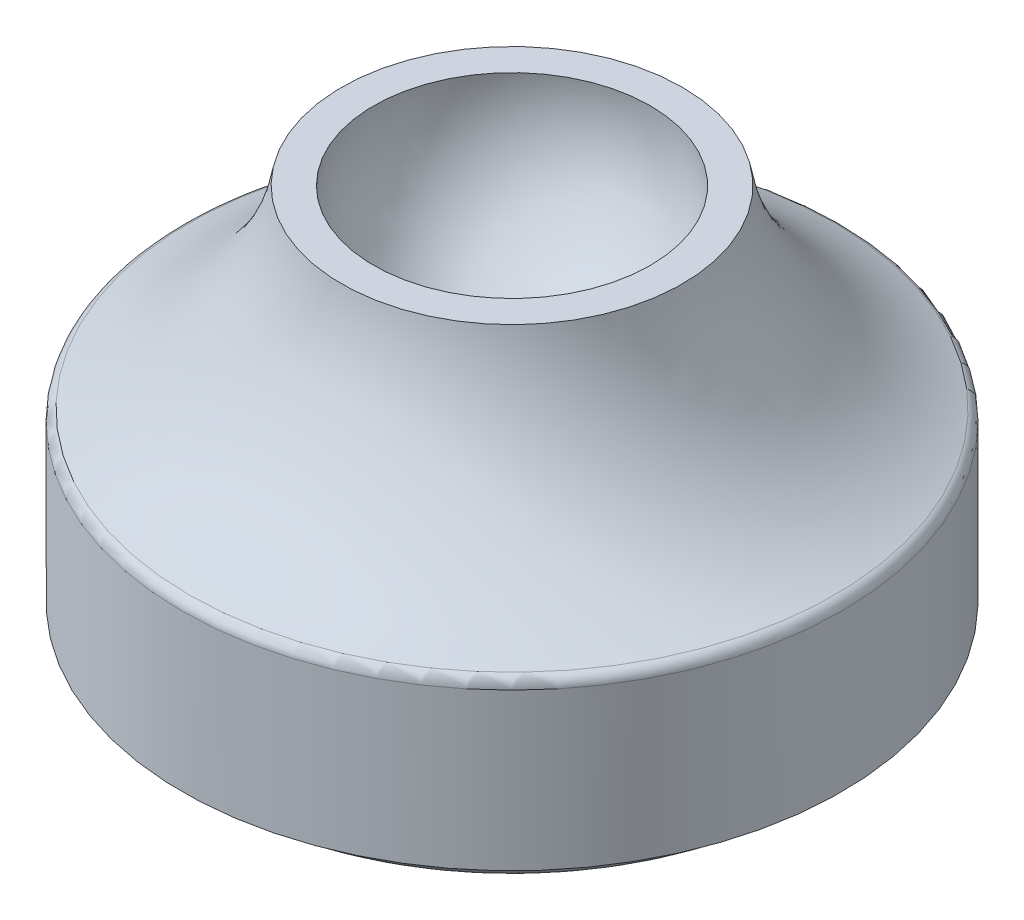
SolidWorks part; units mm, degrees
ref_plane "Front" through (0, 0, 0) normal (0, 0, 1) x (1, 0, 0)
ref_plane "Top" through (0, 0, 0) normal (0, 1, 0) x (1, 0, 0)
ref_plane "Right" through (0, 0, 0) normal (1, 0, 0) x (0, 0, -1)
sketch "Sketch1" plane through (0, 0, 0) normal (0, 0, 1) x (1, 0, 0)
  line L0 (0, 0) -> (26.2862, 0)
  line L1 (26.2862, 0) -> (26.2862, 2.4101)
  line L2 (26.2862, 2.4101) -> (28.7352, 2.4101)
  line L3 (28.7352, 2.4101) -> (28.7352, 16.7262)
  line L4 (14.8575, 33.8411) -> (12.0635, 33.8411)
  line L5 (0, 0) -> (0, 20.0929)
  line L6 (0, 32.2597) -> (12.1667, 32.2597) construction
  arc A0 (14.8575, 33.8411) -> (28.7352, 16.7262) centre (36.7437, 37.4039) ccw
  arc A1 (0, 20.0929) -> (12.0635, 33.8411) centre (0, 32.2597) ccw
revolve "Revolve1" add sketch "Sketch1" angle 360 about L5
fillet "Fillet1" radius 1 2 edges at (0, 16.7262, -28.7352) (0, 0, -26.2862)
